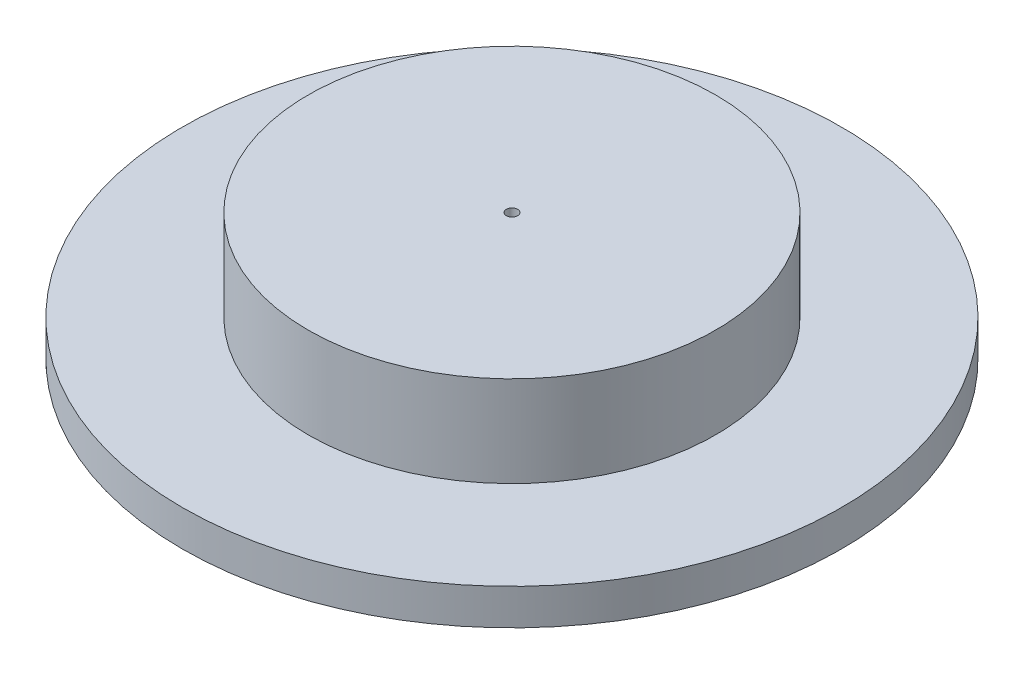
SolidWorks part; units mm, degrees
material "6061-T6 (SS)"
ref_plane "Front Plane" through (0, 0, 0) normal (0, 0, 1) x (1, 0, 0)
ref_plane "Top Plane" through (0, 0, 0) normal (0, 1, 0) x (1, 0, 0)
ref_plane "Right Plane" through (0, 0, 0) normal (1, 0, 0) x (0, 0, -1)
sketch "Sketch1" plane through (0, 0, 0) normal (0, 1, 0) x (1, 0, 0)
  circle A0 centre (0, 0) radius 69.85
  dimension "D1" = 139.7
extrude "Boss-Extrude1" add sketch "Sketch1" along normal blind 7.62
sketch "Sketch3" plane through (0, 0, 0) normal (0, 0, 1) x (1, 0, 0)
  line L0 (0, 7.62) -> (0, 14.1478) construction
  line L1 (69.85, 7.62) -> (-69.85, 7.62) construction
  line L2 (0, 14.1478) -> (31.8735, 14.1478)
  line L3 (31.8735, 14.1478) -> (43.18, 7.62)
  line L4 (69.85, 7.62) -> (-69.85, 7.62) construction
  line L5 (43.18, 7.62) -> (0, 7.62)
  line L6 (0, 7.62) -> (0, 14.1478)
  dimension "D1" = 43.18
  dimension "D2" = 30
  dimension "D3" = 6.5278
revolve "Revolve1" add sketch "Sketch3" angle 360 about L0
sketch "Sketch5" plane through (0, 14.1478, 0) normal (0, 1, 0) x (1, 0, 0)
  circle A4 centre (0, 0) radius 43.18
extrude "Boss-Extrude2" add sketch "Sketch5" along normal blind 12.7 and the other way up to next (14.1478 mm away)
sketch "Sketch6" plane through (0, 26.8478, 0) normal (0, 1, 0) x (1, 0, 0)
  circle A0 centre (0, 0) radius 1.1906
  circle A2 centre (0, 0) radius 43.18
  circle A3 centre (0, 0) radius 43.18
  point P3 (0, 0)
  point P4 (0, 0)
  dimension "D3" = 2.3813
  dimension "D1" = 0
extrude "Cut-Extrude2" cut sketch "Sketch6" against normal blind 17.3228 contours A0
sketch "Sketch7" plane through (0, 0, 0) normal (0, -1, 0) x (1, 0, 0)
  circle A0 centre (0, 0) radius 38.1
  dimension "D1" = 76.2
extrude "Cut-Extrude3" cut sketch "Sketch7" against normal blind 9.525
